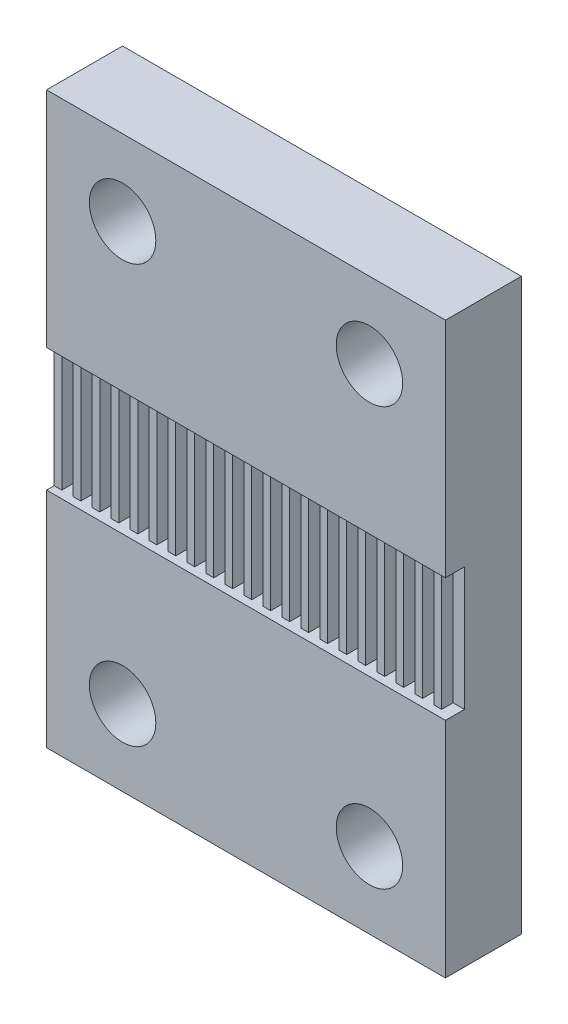
SolidWorks part; units mm, degrees
ref_plane "Front Plane" through (0, 0, 0) normal (0, 0, 1) x (1, 0, 0)
ref_plane "Top Plane" through (0, 0, 0) normal (0, 1, 0) x (1, 0, 0)
ref_plane "Right Plane" through (0, 0, 0) normal (1, 0, 0) x (0, 0, -1)
sketch "Sketch1" plane through (0, 0, 0) normal (0, 0, 1) x (1, 0, 0)
  line L0 (17, 24.25) -> (17, 26)
  line L1 (0, 0) -> (21, 0)
  line L2 (0, 0) -> (0, 30)
  line L3 (0, 30) -> (21, 30)
  line L4 (21, 0) -> (21, 30)
  line L5 (17, 4) -> (17, 5.75)
  line L7 (4, 4) -> (4, 5.75)
  line L8 (4, 24.25) -> (4, 26)
  line L10 (4, 4) -> (4, 26) construction
  line L11 (4, 4) -> (17, 4) construction
  line L12 (4, 26) -> (17, 26) construction
  line L13 (17, 4) -> (17, 26) construction
  circle A0 centre (4, 26) radius 1.75
  circle A1 centre (17, 26) radius 1.75
  circle A2 centre (17, 4) radius 1.75
  circle A3 centre (4, 4) radius 1.75
  dimension "D4" = 3.5
  dimension "D1" = 21
  dimension "D2" = 30
  dimension "D3" = 4
extrude "Boss-Extrude1" add sketch "Sketch1" along normal blind 4 contours L1 L4 L3 L2 A3 A2 A1 A0
sketch "Sketch2" plane through (0, 0, 4) normal (0, 0, 1) x (1, 0, 0)
  line L0 (10.5, 30) -> (10.5, 0) construction
  line L1 (0, 30) -> (21, 30) construction
  line L2 (0, 0) -> (21, 0) construction
  line L3 (21, 0) -> (21, 30) construction
  line L4 (0, 18.25) -> (21, 18.25)
  line L5 (0, 18.25) -> (0, 11.75)
  line L6 (0, 11.75) -> (21, 11.75)
  line L7 (21, 18.25) -> (21, 11.75)
  line L8 (0, 18.25) -> (21, 11.75) construction
  line L9 (0, 11.75) -> (21, 18.25) construction
  point P6 (10.5, 15)
  dimension "D1" = 6.5
extrude "Cut-Extrude1" cut sketch "Sketch2" against normal blind 1
sketch "Sketch3" plane through (0, 0, 3) normal (0, 0, 1) x (1, 0, 0)
  line L0 (0, 11.75) -> (21, 11.75) construction
  line L1 (0, 18.25) -> (0.4, 18.25)
  line L2 (0, 18.25) -> (0, 11.75)
  line L3 (0, 11.75) -> (0.4, 11.75)
  line L4 (0.4, 18.25) -> (0.4, 11.75)
  line L5 (1, 11.75) -> (1.4, 11.75)
  line L6 (1, 18.25) -> (1, 11.75)
  line L7 (1.4, 18.25) -> (1.4, 11.75)
  line L8 (1, 18.25) -> (1.4, 18.25)
  line L9 (2, 11.75) -> (2.4, 11.75)
  line L10 (2, 18.25) -> (2, 11.75)
  line L11 (2.4, 18.25) -> (2.4, 11.75)
  line L12 (2, 18.25) -> (2.4, 18.25)
  line L13 (3, 11.75) -> (3.4, 11.75)
  line L14 (3, 18.25) -> (3, 11.75)
  line L15 (3.4, 18.25) -> (3.4, 11.75)
  line L16 (3, 18.25) -> (3.4, 18.25)
  line L17 (4, 11.75) -> (4.4, 11.75)
  line L18 (4, 18.25) -> (4, 11.75)
  line L19 (4.4, 18.25) -> (4.4, 11.75)
  line L20 (4, 18.25) -> (4.4, 18.25)
  line L21 (5, 11.75) -> (5.4, 11.75)
  line L22 (5, 18.25) -> (5, 11.75)
  line L23 (5.4, 18.25) -> (5.4, 11.75)
  line L24 (5, 18.25) -> (5.4, 18.25)
  line L25 (6, 11.75) -> (6.4, 11.75)
  line L26 (6, 18.25) -> (6, 11.75)
  line L27 (6.4, 18.25) -> (6.4, 11.75)
  line L28 (6, 18.25) -> (6.4, 18.25)
  line L29 (7, 11.75) -> (7.4, 11.75)
  line L30 (7, 18.25) -> (7, 11.75)
  line L31 (7.4, 18.25) -> (7.4, 11.75)
  line L32 (7, 18.25) -> (7.4, 18.25)
  line L33 (8, 11.75) -> (8.4, 11.75)
  line L34 (8, 18.25) -> (8, 11.75)
  line L35 (8.4, 18.25) -> (8.4, 11.75)
  line L36 (8, 18.25) -> (8.4, 18.25)
  line L37 (9, 11.75) -> (9.4, 11.75)
  line L38 (9, 18.25) -> (9, 11.75)
  line L39 (9.4, 18.25) -> (9.4, 11.75)
  line L40 (9, 18.25) -> (9.4, 18.25)
  line L41 (10, 11.75) -> (10.4, 11.75)
  line L42 (10, 18.25) -> (10, 11.75)
  line L43 (10.4, 18.25) -> (10.4, 11.75)
  line L44 (10, 18.25) -> (10.4, 18.25)
  line L45 (11, 11.75) -> (11.4, 11.75)
  line L46 (11, 18.25) -> (11, 11.75)
  line L47 (11.4, 18.25) -> (11.4, 11.75)
  line L48 (11, 18.25) -> (11.4, 18.25)
  line L49 (12, 11.75) -> (12.4, 11.75)
  line L50 (12, 18.25) -> (12, 11.75)
  line L51 (12.4, 18.25) -> (12.4, 11.75)
  line L52 (12, 18.25) -> (12.4, 18.25)
  line L53 (13, 11.75) -> (13.4, 11.75)
  line L54 (13, 18.25) -> (13, 11.75)
  line L55 (13.4, 18.25) -> (13.4, 11.75)
  line L56 (13, 18.25) -> (13.4, 18.25)
  line L57 (14, 11.75) -> (14.4, 11.75)
  line L58 (14, 18.25) -> (14, 11.75)
  line L59 (14.4, 18.25) -> (14.4, 11.75)
  line L60 (14, 18.25) -> (14.4, 18.25)
  line L61 (15, 11.75) -> (15.4, 11.75)
  line L62 (15, 18.25) -> (15, 11.75)
  line L63 (15.4, 18.25) -> (15.4, 11.75)
  line L64 (15, 18.25) -> (15.4, 18.25)
  line L65 (16, 11.75) -> (16.4, 11.75)
  line L66 (16, 18.25) -> (16, 11.75)
  line L67 (16.4, 18.25) -> (16.4, 11.75)
  line L68 (16, 18.25) -> (16.4, 18.25)
  line L69 (17, 11.75) -> (17.4, 11.75)
  line L70 (17, 18.25) -> (17, 11.75)
  line L71 (17.4, 18.25) -> (17.4, 11.75)
  line L72 (17, 18.25) -> (17.4, 18.25)
  line L73 (18, 11.75) -> (18.4, 11.75)
  line L74 (18, 18.25) -> (18, 11.75)
  line L75 (18.4, 18.25) -> (18.4, 11.75)
  line L76 (18, 18.25) -> (18.4, 18.25)
  line L77 (19, 11.75) -> (19.4, 11.75)
  line L78 (19, 18.25) -> (19, 11.75)
  line L79 (19.4, 18.25) -> (19.4, 11.75)
  line L80 (19, 18.25) -> (19.4, 18.25)
  line L81 (20, 11.75) -> (20.4, 11.75)
  line L82 (20, 18.25) -> (20, 11.75)
  line L83 (20.4, 18.25) -> (20.4, 11.75)
  line L84 (20, 18.25) -> (20.4, 18.25)
  dimension "D1" = 0.4
  dimension "D2" = 21
extrude "Boss-Extrude2" add sketch "Sketch3" along normal blind 0.6
